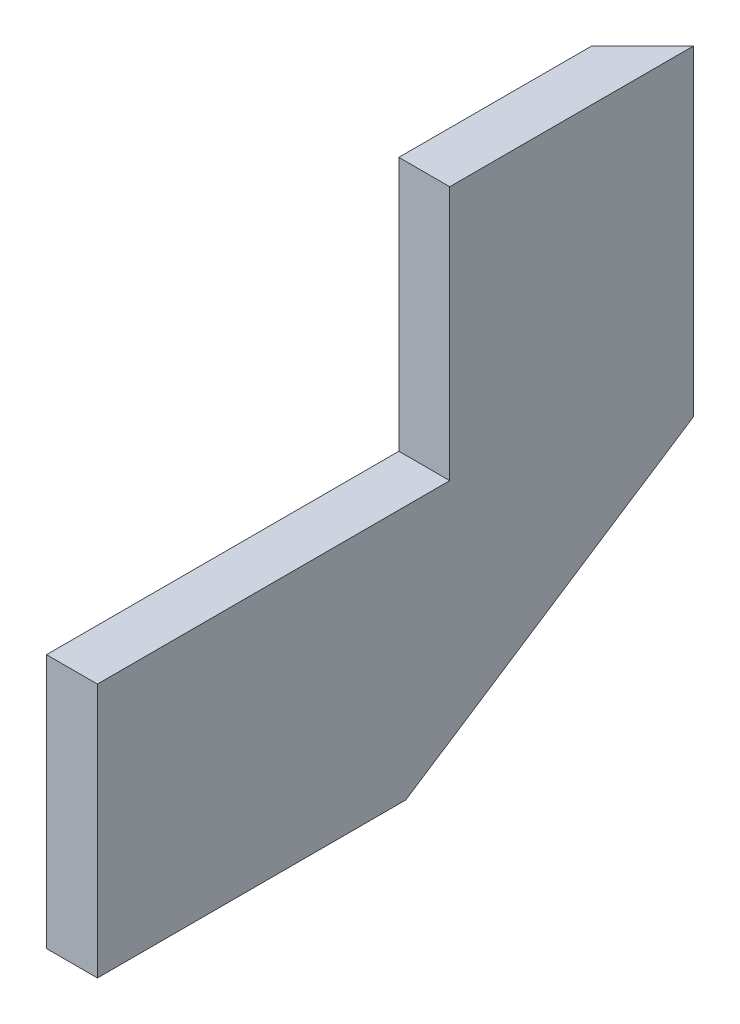
SolidWorks part; units mm, degrees
ref_plane "Front Plane" through (0, 0, 0) normal (0, 0, 1) x (1, 0, 0)
ref_plane "Top Plane" through (0, 0, 0) normal (0, 1, 0) x (1, 0, 0)
ref_plane "Right Plane" through (0, 0, 0) normal (1, 0, 0) x (0, 0, -1)
sketch "Sketch1" plane through (0, 0, 0) normal (1, 0, 0) x (0, 0, -1)
  line L0 (230.7901, 0) -> (446.0575, 140.7778)
  line L6 (0, 0) -> (0, 190.5)
  line L7 (0, 190.5) -> (263.652, 190.5)
  line L8 (446.0575, 381) -> (446.0575, 140.7778)
  line L10 (263.652, 190.5) -> (263.652, 381)
  line L11 (263.652, 381) -> (446.0575, 381)
  line L21 (446.0575, 381) -> (263.652, 381)
  line L25 (263.652, 190.5) -> (241.3, 190.5)
  line L26 (263.652, 190.5) -> (263.652, 381)
  line L29 (241.3, 190.5) -> (0, 190.5)
  line L34 (0, 0) -> (0, 190.5)
  line L41 (0, 0) -> (230.7901, 0)
  line L42 (0, 0) -> (0, 190.5)
  line L43 (0, 190.5) -> (263.652, 190.5)
  dimension "D2" = 190.5
  dimension "D3" = 190.5
  dimension "D4" = 263.652
  dimension "D5" = 240.2222
  dimension "D6" = 182.4055
  dimension "D10" = 285.75
  dimension "D12" = 141.4479
  dimension "D13" = 230.7901
extrude "Boss-Extrude2" add sketch "Sketch1" along normal blind 38.1
sketch "Sketch2" plane through (0, 381, 0) normal (0, 1, 0) x (1, 0, 0)
  line L0 (38.1, 446.0575) -> (0, 407.9575)
  line L3 (0, 263.652) -> (0, 446.0575) construction
  line L4 (0, 407.9575) -> (0, 446.0575)
  line L5 (0, 446.0575) -> (38.1, 446.0575)
extrude "Cut-Extrude1" cut sketch "Sketch2" against normal up to next
